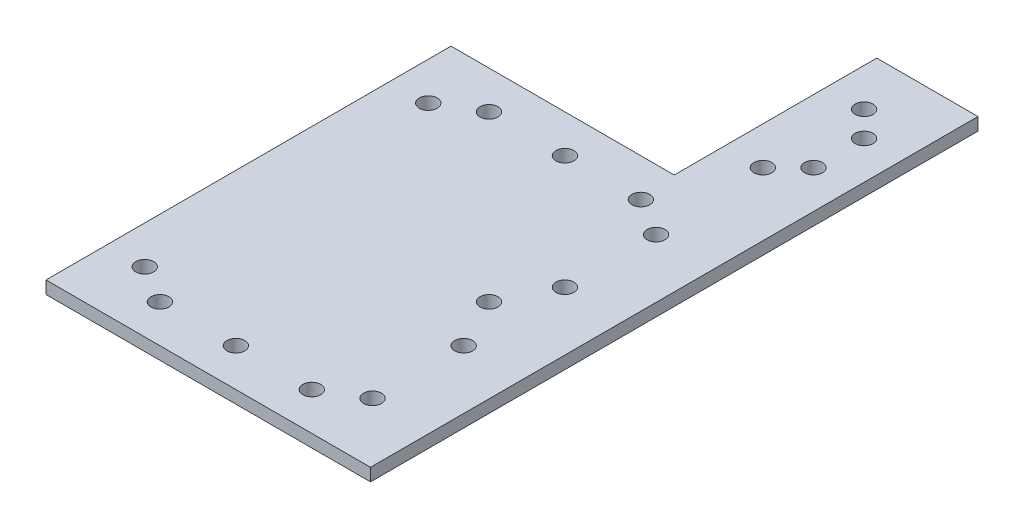
SolidWorks part; units mm, degrees
ref_plane "Front Plane" through (0, 0, 0) normal (0, 0, 1) x (1, 0, 0)
ref_plane "Top Plane" through (0, 0, 0) normal (0, 1, 0) x (1, 0, 0)
ref_plane "Right Plane" through (0, 0, 0) normal (1, 0, 0) x (0, 0, -1)
sketch "Sketch1" plane through (0, 0, 0) normal (0, 1, 0) x (1, 0, 0)
  line L0 (-19.05, -41.275) -> (19.05, -41.275) construction
  line L1 (38.1, 50.8) -> (-38.1, 50.8)
  line L2 (38.1, 50.8) -> (38.1, -50.8)
  line L3 (38.1, -50.8) -> (-38.1, -50.8)
  line L4 (-38.1, 50.8) -> (-38.1, -50.8)
  line L5 (38.1, 50.8) -> (-38.1, -50.8) construction
  line L6 (38.1, -50.8) -> (-38.1, 50.8) construction
  line L7 (0, 0) -> (0, -41.275) construction
  line L8 (28.575, -35.56) -> (-28.575, -35.56) construction
  line L9 (0, 0) -> (38.1, 0) construction
  line L10 (28.575, 12.7) -> (28.575, 0) construction
  line L11 (28.575, 0) -> (28.575, -12.7) construction
  circle A0 centre (-19.05, -41.275) radius 2.25
  circle A1 centre (19.05, -41.275) radius 2.25
  circle A2 centre (28.575, -35.56) radius 2.25
  circle A3 centre (-28.575, -35.56) radius 2.25
  circle A4 centre (28.575, 35.56) radius 2.25
  circle A5 centre (19.05, 41.275) radius 2.25
  circle A6 centre (-28.575, 35.56) radius 2.25
  circle A7 centre (-19.05, 41.275) radius 2.25
  circle A8 centre (0, -41.275) radius 2.25
  circle A9 centre (0, 41.275) radius 2.25
  circle A12 centre (28.575, 12.7) radius 2.25
  circle A13 centre (28.575, -12.7) radius 2.25
  circle A14 centre (22.23, 0) radius 2.25
  point P0 (0, 0)
  point P16 (0, -35.56)
  dimension "D3" = 9.525
  dimension "D5" = 4.5
  dimension "D8" = 12.7
  dimension "D9" = 12.69
  dimension "D1" = 101.6
  dimension "D2" = 76.2
  dimension "D4" = 9.525
  dimension "D6" = 19.05
  dimension "D7" = 15.24
extrude "Boss-Extrude1" add sketch "Sketch1" along normal blind 3.175
sketch "Sketch2" plane through (0, 3.175, 0) normal (0, 1, 0) x (1, 0, 0)
  line L0 (38.1, -50.8) -> (43.3, -50.8)
  line L1 (43.3, -50.8) -> (43.3, 101.6)
  line L2 (43.3, 101.6) -> (17.9, 101.6)
  line L3 (17.9, 101.6) -> (17.9, 50.8)
  line L4 (38.1, 50.8) -> (-38.1, 50.8) construction
  line L5 (17.9, 50.8) -> (38.1, 50.8)
  line L6 (38.1, 50.8) -> (38.1, -50.8)
  dimension "D1" = 5.2
  dimension "D2" = 25.4
  dimension "D3" = 50.8
extrude "Boss-Extrude2" add sketch "Sketch2" against normal up to surface (3.175 mm away) up to face at (28.575, 0, 14.95)
sketch "Sketch3" plane through (0, 3.175, 0) normal (0, 1, 0) x (1, 0, 0)
  line L0 (17.9, 101.6) -> (17.9, 50.8) construction
  line L2 (27.425, 88.9) -> (27.425, 101.6) construction
  line L3 (43.3, 101.6) -> (17.9, 101.6) construction
  line L4 (27.425, 63.5) -> (27.425, 50.8) construction
  line L5 (17.9, 50.8) -> (-38.1, 50.8) construction
  line L6 (43.3, -50.8) -> (43.3, 101.6) construction
  line L7 (33.77, 82.55) -> (33.77, 69.85) construction
  line L8 (27.425, 88.9) -> (27.425, 63.5) construction
  line L9 (33.77, 76.2) -> (27.425, 76.2) construction
  circle A0 centre (33.77, 82.55) radius 2.25
  circle A1 centre (33.77, 69.85) radius 2.25
  circle A2 centre (27.425, 88.9) radius 2.25
  circle A3 centre (27.425, 63.5) radius 2.25
  dimension "D1" = 4.5
  dimension "D2" = 25.4
  dimension "D3" = 9.525
  dimension "D4" = 9.53
  dimension "D5" = 12.7
extrude "Cut-Extrude1" cut sketch "Sketch3" against normal blind 10
